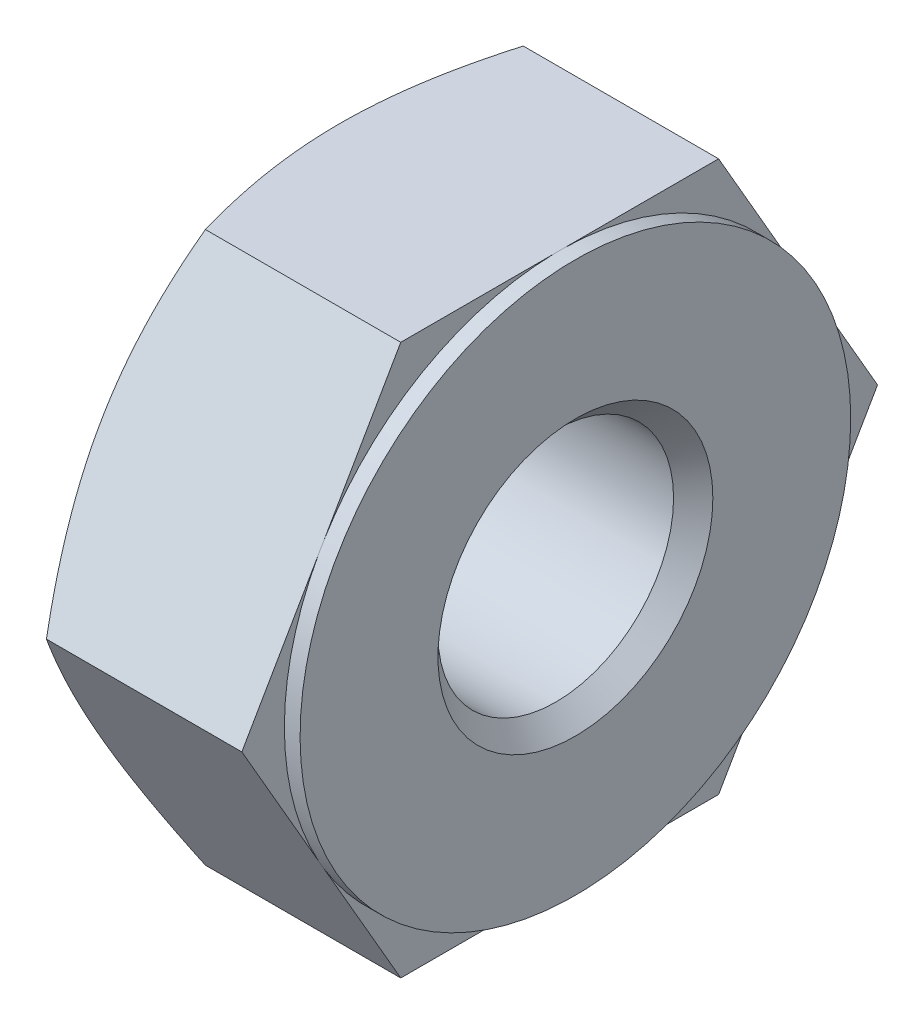
SolidWorks part; units mm, degrees
ref_plane "Front Plane" through (0, 0, 0) normal (0, 0, 1) x (1, 0, 0)
ref_plane "Top Plane" through (0, 0, 0) normal (0, 1, 0) x (1, 0, 0)
ref_plane "Right Plane" through (0, 0, 0) normal (1, 0, 0) x (0, 0, -1)
sketch "Sketch6" plane through (0, 0, 0) normal (0, 1, 0) x (1, 0, 0)
  line L9 (9.0152, -1.9501) -> (9.0152, -5.9969)
  line L14 (6.2152, -2.4916) -> (6.5278, -1.9501)
  line L17 (6.5278, -1.9501) -> (9.0152, -1.9501)
  line L25 (6.2152, -5.9969) -> (9.0152, -5.9969)
  line L27 (6.2152, -2.4916) -> (6.2152, -5.9969)
  line L28 (5.1488, -5.9969) -> (11.6487, -5.9969) construction
  dimension "D1" = 2.4874
  dimension "D2" = 0.6252
  dimension "D3" = 120
  dimension "D5" = 3.5053
revolve "Revolve10" add sketch "Sketch6" angle 360 about L28
sketch "Sketch14" plane through (9.0152, 0, 0) normal (1, 0, 0) x (0, 0, -1)
  line L1 (-1.9501, 0) -> (-3.9735, 3.5046)
  line L2 (-3.9735, 3.5046) -> (-8.0203, 3.5046)
  line L3 (-8.0203, 3.5046) -> (-10.0437, 0)
  line L4 (-10.0437, 0) -> (-8.0203, -3.5046)
  line L5 (-8.0203, -3.5046) -> (-3.9735, -3.5046)
  line L6 (-3.9735, -3.5046) -> (-1.9501, 0)
  circle A1 centre (-5.9969, 0) radius 4.0468
  point P10 (0, 0)
  circle M8 centre (-5.9969, 0) radius 4.0468
extrude "Cut-Extrude8" cut sketch "Sketch14" against normal blind 3.5 contours L2 M8 | L3 M8 | L4 M8 | L5 M8 | L6 M8 | L1 M8
sketch "Sketch16" plane through (9.0152, 0, 0) normal (1, 0, 0) x (0, 0, -1)
  line L0 (-5.9969, 3.5046) -> (-5.9969, -3.5046) construction
  line L1 (-3.9735, 3.5046) -> (-8.0203, 3.5046) construction
  line L2 (-8.0203, -3.5046) -> (-3.9735, -3.5046) construction
  circle A0 centre (-5.9969, 0) radius 3.5053
extrude "Boss-Extrude10" add sketch "Sketch16" along normal blind 0.2
sketch "Sketch17" plane through (9.2152, 0, 0) normal (1, 0, 0) x (0, 0, -1)
  line L0 (-5.9969, 3.5053) -> (-5.9969, -3.5053) construction
  circle A0 centre (-5.9969, 0) radius 3.5053 construction
  circle A1 centre (-5.9969, 0) radius 1.5
  dimension "D1" = 3
extrude "Cut-Extrude9" cut sketch "Sketch17" against normal blind 5
chamfer "Chamfer2" distance 0.25 angle 45 2 edges at (9.2152, 0, 4.4969) (6.2152, 0, 4.4969)
